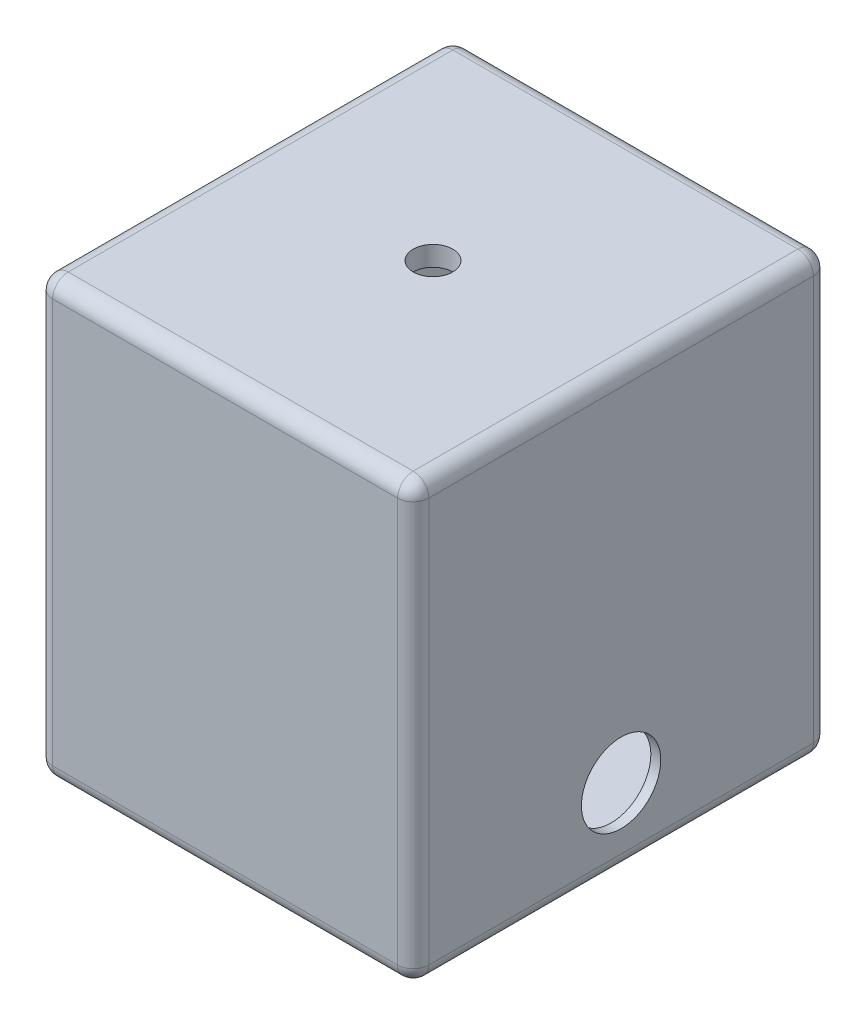
SolidWorks part; units mm, degrees
material "ABS PC"
ref_plane "Front Plane" through (0, 0, 0) normal (0, 0, 1) x (1, 0, 0)
ref_plane "Top Plane" through (0, 0, 0) normal (0, 1, 0) x (1, 0, 0)
ref_plane "Right Plane" through (0, 0, 0) normal (1, 0, 0) x (0, 0, -1)
sketch "Sketch1" plane through (0, 0, 0) normal (0, 1, 0) x (1, 0, 0)
  line L1 (-120.65, -133.35) -> (120.65, -133.35)
  line L2 (-120.65, -133.35) -> (-120.65, 133.35)
  line L3 (-120.65, 133.35) -> (120.65, 133.35)
  line L4 (120.65, -133.35) -> (120.65, 133.35)
  line L5 (-120.65, -133.35) -> (120.65, 133.35) construction
  line L6 (-120.65, 133.35) -> (120.65, -133.35) construction
  point P0 (0, 0)
  dimension "D1" = 266.7
  dimension "D2" = 241.3
extrude "Boss-Extrude1" add sketch "Sketch1" along normal blind 266.7
sketch "Sketch8" plane through (0, 266.7, 0) normal (0, 1, 0) x (1, 0, 0)
  line L1 (-114.3, -127) -> (114.3, -127)
  line L2 (-114.3, -127) -> (-114.3, 127)
  line L3 (-114.3, 127) -> (114.3, 127)
  line L4 (114.3, -127) -> (114.3, 127)
  line L5 (-114.3, -127) -> (114.3, 127) construction
  line L6 (-114.3, 127) -> (114.3, -127) construction
  point P0 (0, 0)
  dimension "D1" = 228.6
  dimension "D2" = 254
extrude "Cut-Extrude4" cut sketch "Sketch8" against normal blind 254
sketch "Sketch9" plane through (0, 266.7, 0) normal (0, 1, 0) x (1, 0, 0)
  line L1 (-120.65, -133.35) -> (120.65, -133.35)
  line L2 (-120.65, -133.35) -> (-120.65, 133.35)
  line L3 (-120.65, 133.35) -> (120.65, 133.35)
  line L4 (120.65, -133.35) -> (120.65, 133.35)
  line L5 (-120.65, -133.35) -> (120.65, 133.35) construction
  line L6 (-120.65, 133.35) -> (120.65, -133.35) construction
  point P0 (0, 0)
extrude "Boss-Extrude3" add sketch "Sketch9" along normal blind 12.7
fillet "Fillet4" radius 10 12 edges at (0, 0, 133.35) (-120.65, 139.7, 133.35) (-120.65, 0, 0) (0, 279.4, 133.35) (-120.65, 279.4, 0) (0, 279.4, -133.35) (-120.65, 139.7, -133.35) (0, 0, -133.35) (120.65, 0, 0) (120.65, 139.7, -133.35) (120.65, 139.7, 133.35) (120.65, 279.4, 0)
sketch "Sketch10" plane through (120.65, 0, 0) normal (1, 0, 0) x (0, 0, -1)
  circle A0 centre (0, 49.5397) radius 25.451
  dimension "D1" = 50.9021
extrude "Cut-Extrude5" cut sketch "Sketch10" against normal blind 12.7
sketch "Sketch11" plane through (0, 279.4, 0) normal (0, 1, 0) x (1, 0, 0)
  circle A0 centre (0, 0) radius 12.7
  dimension "D1" = 25.4
extrude "Cut-Extrude6" cut sketch "Sketch11" against normal blind 12.7
